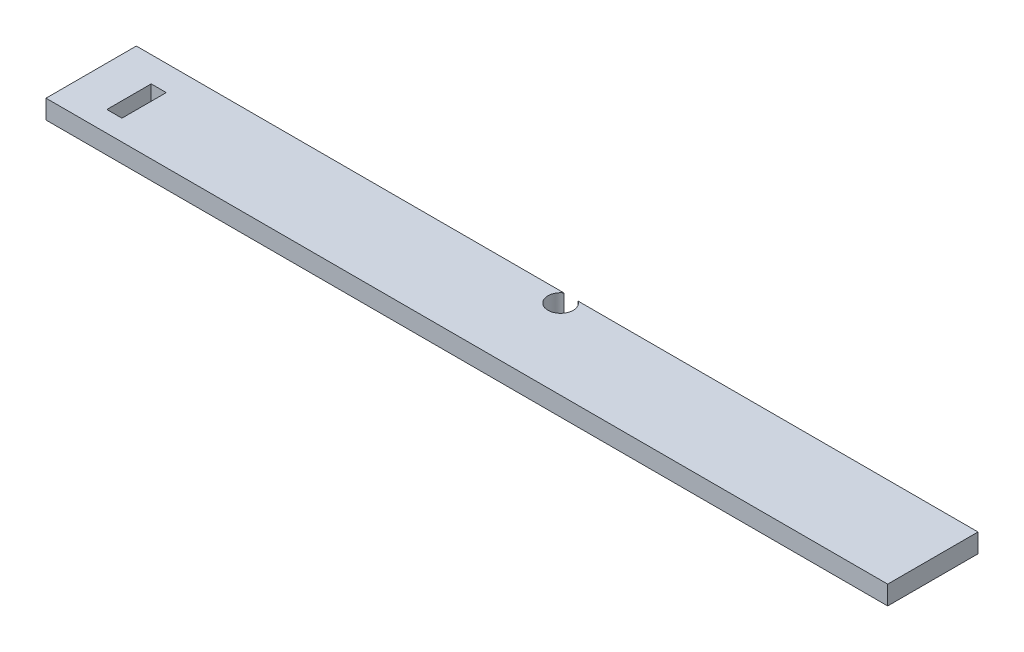
SolidWorks part; units mm, degrees
material "Oak"
ref_plane "Front Plane" through (0, 0, 0) normal (0, 0, 1) x (1, 0, 0)
ref_plane "Top Plane" through (0, 0, 0) normal (0, 1, 0) x (1, 0, 0)
ref_plane "Right Plane" through (0, 0, 0) normal (1, 0, 0) x (0, 0, -1)
sketch "Sketch1" plane through (0, 0, 0) normal (0, 1, 0) x (1, 0, 0)
  line L1 (0, 0) -> (846.328, 0)
  line L2 (0, 0) -> (0, 90.8304)
  line L3 (0, 90.8304) -> (846.328, 90.8304)
  line L4 (846.328, 0) -> (846.328, 90.8304)
  dimension "D1" = 90.8304
  dimension "D2" = 846.328
extrude "Boss-Extrude1" add sketch "Sketch1" along normal blind 19.05
sketch "Sketch2" plane through (0, 0, 0) normal (0, -1, 0) x (1, 0, 0)
  line L3 (0, -90.8304) -> (0, 0) construction
  line L6 (846.328, -90.8304) -> (0, -90.8304) construction
  circle A0 centre (437.1086, -80.3402) radius 12.7
  dimension "D1" = 25.4
  dimension "D2" = 437.1086
  dimension "D3" = 10.4902
extrude "Cut-Extrude4" cut sketch "Sketch2" against normal through all
sketch "Sketch4" plane through (0, 0, 0) normal (0, -1, 0) x (1, 0, 0)
  line L1 (55.6027, -65.3402) -> (40.446, -65.3402)
  line L2 (55.6027, -65.3402) -> (55.6027, -20.7616)
  line L3 (55.6027, -20.7616) -> (40.446, -20.7616)
  line L4 (40.446, -65.3402) -> (40.446, -20.7616)
extrude "Cut-Extrude5" cut sketch "Sketch4" against normal through all
